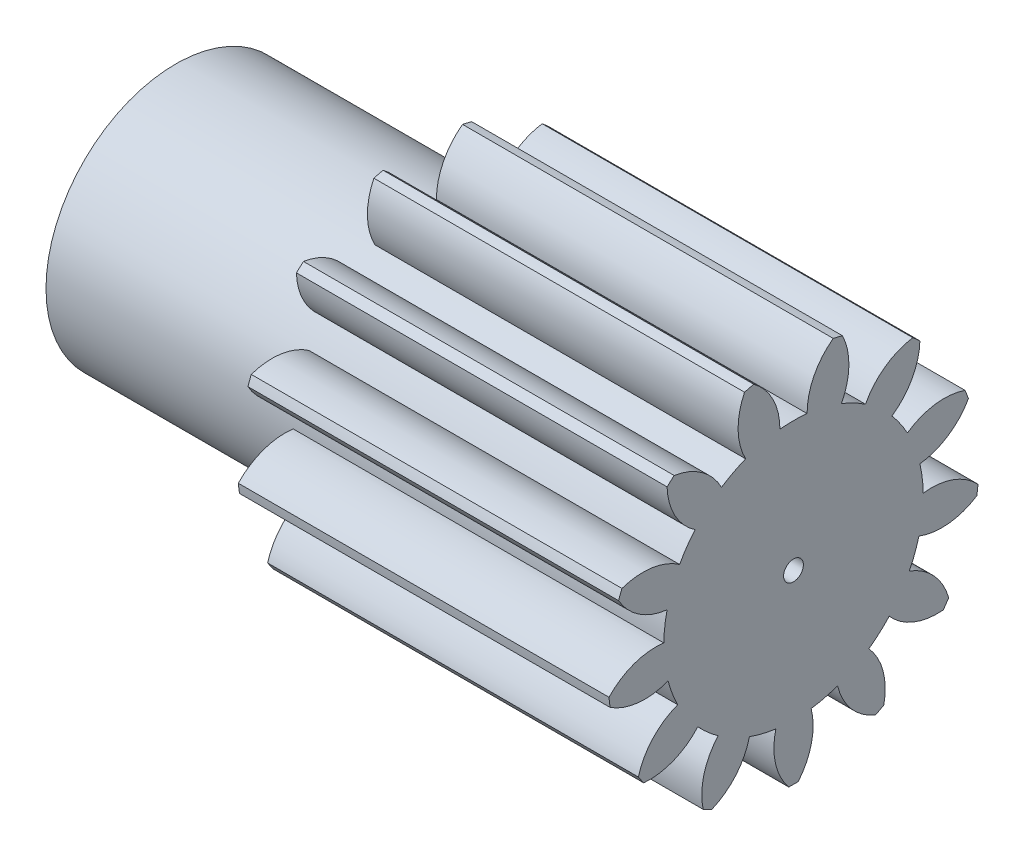
SolidWorks part; units mm, degrees
ref_plane "Plane1" through (0, 0, 0) normal (0, 0, 1) x (1, 0, 0)
ref_plane "Plane2" through (0, 0, 0) normal (0, 1, 0) x (1, 0, 0)
ref_plane "Plane3" through (0, 0, 0) normal (1, 0, 0) x (0, 0, -1)
sketch "HoldingSke" plane through (0, 0, 0) normal (0, 1, 0) x (1, 0, 0)
  line L0 (0, 0) -> (0.9744, -0.225)
  line L1 (-15, 0) -> (100, 0) construction
  line L2 (0, 0) -> (-2.1039, 2.3779)
  line L3 (0, 0) -> (-11.863, 4.5341)
  line L4 (0, 0) -> (8.4147, 1.9427)
  line L5 (0, 0) -> (-23.4238, -8.7364)
  line L6 (0, 0) -> (-12.4344, -8.3896)
  line L7 (-2.1039, 2.3779) -> (3.2774, 26.7919)
  line L8 (-76.2, 54.61) -> (-76.1, 54.61)
  line L9 (-71.009, 38.7566) -> (-53.1078, 45.2721)
  line L10 (-76.2, 71.12) -> (104.1128, 71.12)
  line L11 (0, 0) -> (-15, 0)
  line L12 (-76.2, 101.6) -> (-76.162, 101.6)
  line L13 (24.9733, 27.94) -> (52.9518, 28.4284)
  line L14 (24.9733, 27.94) -> (24.9743, 27.94)
  line L15 (24.9733, 27.94) -> (100.4006, 29.5858)
  line L16 (-63.627, -1) -> (-12.827, -1)
  circle A0 centre (0, 0) radius 0.4
  circle A1 centre (0, 0) radius 5.249
  circle A2 centre (0, 0) radius 37.5
  circle A3 centre (0, 0) radius 0.4
  dimension "MHD" = 10.498
  dimension "Hub_dia" = 75
  dimension "Bore" = 0.8
  dimension "MBD" = 0.8
  dimension "Num_teeth" = 13
  dimension "Pitch" = 1
  dimension "Overall_len" = 25
  dimension "Show_teeth" = 13
  dimension "Thickness" = 15
  dimension "OAL" = 25.0001
  dimension "T_dim" = 0.1
  dimension "Ap" = 20
  dimension "H" = 19.05
  dimension "Pitch_radius" = 180.3128
  dimension "Width" = 15
  dimension "Backlash" = 0.038
  dimension "Addendum_fac" = 1
  dimension "Dedendum_fac" = 1.25
  dimension "Clearance_fac" = 0.25
  dimension "Dedendum_add" = 0.001
  dimension "Module" = 1
sketch "BasProSke" plane through (0, 0, 0) normal (0, 1, 0) x (1, 0, 0)
  line L0 (-10, 0) -> (60, 0) construction
  line L1 (0, 0) -> (0, 7.5)
  line L2 (0, 0) -> (15, 0)
  line L3 (15, 0) -> (15, 7.5)
  line L4 (15, 7.5) -> (0, 7.5)
  dimension "Thickness" = 15
  dimension "Diameter" = 15
revolve "Base-Revolve" add sketch "BasProSke" angle 360 about L0
sketch "TooCutSke" plane through (0, 0, 0) normal (1, 0, 0) x (0, 0, -1)
  line L1 (0, 0) -> (0, 107) construction
  line L2 (0, 0) -> (-0.8499, 6.4442) construction
  line L3 (0, 0) -> (-3.0921, 12.5452) construction
  line L4 (-0.8499, 6.4442) -> (-1.5461, 6.2726) construction
  arc A0 (0.5505, 5.2201) -> (-0.5505, 5.2201) centre (0, 0) ccw
  arc A1 (1.6352, 7.3456) -> (-1.6352, 7.3456) centre (0, 0) ccw
  circle A2 centre (0, 0) radius 6.5 construction
  circle A3 centre (0, 0) radius 6.108 construction
  arc A4 (-0.5505, 5.2201) -> (-1.6352, 7.3456) centre (-3.1505, 5.2328) ccw
  arc A5 (1.6352, 7.3456) -> (0.5505, 5.2201) centre (3.1505, 5.2328) ccw
  dimension "Root_dia" = 10.498
  dimension "Overcut_dia" = 15.0508
  dimension "Pitch_dia" = 13
  dimension "Base_dia" = 12.216
  dimension "Flank_rad" = 2.6
  dimension "Half_ang" = 13.846
  dimension "Half_CT" = 0.717
extrude "ToothCut" cut sketch "TooCutSke" along normal through all
fillet "Breaks" [suppressed] radius 0.02
fillet "RootFillets" [suppressed] radius 0.251
pattern_circular "TeethCuts" count 13 every 27.692 about axis through (-10, 0, 0) along (1, 0, 0) of "ToothCut", "RootFillets", "Breaks"
sketch "HubNeaOneSke" plane through (0, 0, 0) normal (-1, 0, 0) x (0, 0, 1)
  circle A0 centre (0, 0) radius 5.249
  dimension "Diameter" = 10.498
extrude "HubNearOne" add sketch "HubNeaOneSke" along normal blind 10.0001
sketch "HubNeaBotSke" plane through (0, 0, 0) normal (-1, 0, 0) x (0, 0, 1)
  circle A0 centre (0, 0) radius 5.249
  dimension "Diameter" = 10.498
extrude "HubNearBoth" [suppressed] add sketch "HubNeaBotSke" along normal blind 5
ref_plane "FarPln" through (15, 0, 0) normal (1, 0, 0) x (0, 0, -1)
sketch "HubFarSke" plane through (15, 0, 0) normal (1, 0, 0) x (0, 0, -1)
  circle A0 centre (0, 0) radius 5.249
  dimension "Diameter" = 10.498
extrude "HubFar" [suppressed] add sketch "HubFarSke" along normal blind 5
sketch "BorSke" plane through (0, 0, 0) normal (1, 0, 0) x (0, 0, -1)
  circle A0 centre (0, 0) radius 0.4
  dimension "Diameter" = 0.8
extrude "Bore" cut sketch "BorSke" along normal mid plane 50.0001
sketch "KeySke" plane through (0, 0, 0) normal (1, 0, 0) x (0, 0, -1)
  line L0 (-0.05, 0) -> (-0.05, 0.5)
  line L1 (-0.05, 0.5) -> (0.05, 0.5)
  line L2 (0.05, 0.5) -> (0.05, 0)
  line L3 (0, 0) -> (0, 34) construction
  line L4 (-0.05, 0) -> (0.05, 0)
  dimension "Offset" = 0.5
  dimension "Width" = 0.1
extrude "Keyway" [suppressed] cut sketch "KeySke" along normal mid plane 50.0001
pattern_circular "Keyway2" [suppressed] count 2 every 90 about axis through (-10, 0, 0) along (1, 0, 0)
equation "' \"Module@HoldingSke\" = 6.35"
equation "' \"Num_teeth@HoldingSke\" = 12"
equation "' \"Ap@HoldingSke\" =  20"
equation "' \"Ap@HoldingSke\" = 20"
equation "' \"Width@HoldingSke\" = 0.5 * 25.4"
equation "' \"Hub_dia@HoldingSke\"= 1 * 25.4"
equation "' \"Hub_dia@HoldingSke\" = 1 * 25.4"
equation "' \"Overall_len@HoldingSke\" = 1.0 * 25.4"
equation "' \"Bore@HoldingSke\" = 0.75 * 25.4"
equation "' \"T_dim@HoldingSke\" = 0.1 * 25.4"
equation "' \"Width@KeySke\" = 0.25 * 25.4"
equation "' \"Show_teeth@HoldingSke\" = 13"
equation "' \"Backlash@HoldingSke\" = 0.009 * 25.4"
equation "' \"Addendum_fac@HoldingSke\" = 1.0"
equation "' \"Dedendum_fac@HoldingSke\" = 1.25"
equation "' \"Dedendum_add@HoldingSke\" = 0.00005 * 25.4"
equation "' \"Clearance_fac@HoldingSke\" = 0.25"
equation "\"Pitch@HoldingSke\" = 1 / \"Module@HoldingSke\""
equation "\"Overcut_dia@TooCutSke\" = (\"Num_teeth@HoldingSke\" + 2 * \"Addendum_fac@HoldingSke\") / \"Pitch@HoldingSke\" + 0.002 * 25.4"
equation "\"Pitch_dia@TooCutSke\" = \"Num_teeth@HoldingSke\" / \"Pitch@HoldingSke\""
equation "\"Base_dia@TooCutSke\" = \"Num_teeth@HoldingSke\" / \"Pitch@HoldingSke\" * cos((\"Ap@HoldingSke\"  * 3.14159265 / 180))"
equation "\"Root_dia@TooCutSke\" = (\"Num_teeth@HoldingSke\" + 2) / \"Pitch@HoldingSke\" - 2 * (\"Addendum_fac@HoldingSke\" + \"Dedendum_fac@HoldingSke\") / \"Pitch@HoldingSke\" - \"Dedendum_add@HoldingSke\" * 2"
equation "\"Half_ang@TooCutSke\" = 180 / \"Num_teeth@HoldingSke\""
equation "\"Half_CT@TooCutSke\" = \"Num_teeth@HoldingSke\" / \"Pitch@HoldingSke\" * sin((3.14159265 / 2 / \"Num_teeth@HoldingSke\")) / 2 - 7 * \"Backlash@HoldingSke\" / 4"
equation "\"Flank_rad@TooCutSke\" = \"Num_teeth@HoldingSke\" / \"Pitch@HoldingSke\" / 5"
equation "\"Radius@RootFillets\" = \"Clearance_fac@HoldingSke\" / \"Pitch@HoldingSke\" + \"Dedendum_add@HoldingSke\""
equation "\"Break_rad@Breaks\" = 0.02 / \"Pitch@HoldingSke\""
equation "\"Thickness@HoldingSke\" = \"Width@HoldingSke\""
equation "\"OAL@HoldingSke\" = \"Thickness@HoldingSke\""
equation "\"MHD@HoldingSke\" = (\"Num_teeth@HoldingSke\" + 2) / \"Pitch@HoldingSke\" - 2 * (\"Addendum_fac@HoldingSke\" + \"Dedendum_fac@HoldingSke\")  / \"Pitch@HoldingSke\" - \"Dedendum_add@HoldingSke\" * 2"
equation "\"MBD@HoldingSke\" = (\"Num_teeth@HoldingSke\" + 2) / \"Pitch@HoldingSke\" - 2 * (\"Addendum_fac@HoldingSke\" + \"Dedendum_fac@HoldingSke\")  / \"Pitch@HoldingSke\" - \"Dedendum_add@HoldingSke\" * 2 - 0.002 * 25.4"
equation "\"MHD@HoldingSke\" = ((sgn( \"MHD@HoldingSke\" - \"Hub_dia@HoldingSke\" )-1)*( \"MHD@HoldingSke\" - \"Hub_dia@HoldingSke\" ))/-2+ \"Hub_dia@HoldingSke\""
equation "\"MBD@HoldingSke\" = ((sgn( \"MBD@HoldingSke\" - \"Bore@HoldingSke\" )-1)*( \"MBD@HoldingSke\" - \"Bore@HoldingSke\" ))/-2+ \"Bore@HoldingSke\""
equation "\"OAL@HoldingSke\" = ((sgn( \"OAL@HoldingSke\" - \"Overall_len@HoldingSke\" )+1)*( \"OAL@HoldingSke\" - \"Overall_len@HoldingSke\" ))/2 + \"Overall_len@HoldingSke\" + 0.000002 * 25.4"
equation "\"Num_teeth@TeethCuts\" = int( \"Show_teeth@HoldingSke\" ) + 1"
equation "\"Num_teeth@TeethCuts\" = ((sgn( \"Num_teeth@TeethCuts\" - \"Num_teeth@HoldingSke\" )-1)*( \"Num_teeth@TeethCuts\" - \"Num_teeth@HoldingSke\" ))/-2+ \"Num_teeth@HoldingSke\""
equation "\"Num_teeth@TeethCuts\" = ((sgn( \"Num_teeth@TeethCuts\" - 2.0)+1)*( \"Num_teeth@TeethCuts\" - 2.0))/2 +2.0"
equation "\"Angle@TeethCuts\" = 360.0 / \"Num_teeth@HoldingSke\""
equation "\"Diameter@BasProSke\" = (\"Num_teeth@HoldingSke\" + 2 * \"Addendum_fac@HoldingSke\") / \"Pitch@HoldingSke\""
equation "\"Thickness@BasProSke\"  = \"Thickness@HoldingSke\""
equation "' \"Fillet_rad@BasProSke\" =  \"Thickness@HoldingSke\" * 0.05"
equation "' \"Fillet_rad@BasProSke\" = \"Thickness@HoldingSke\" * 0.05"
equation "\"MHD@HoldingSke\" = ((sgn( \"MHD@HoldingSke\" - \"Root_dia@TooCutSke\" )-1)*( \"MHD@HoldingSke\" - \"Root_dia@TooCutSke\" ))/-2+ \"Root_dia@TooCutSke\""
equation "\"Diameter@HubNeaOneSke\" = \"MHD@HoldingSke\""
equation "\"Length@HubNearOne\" = \"OAL@HoldingSke\" - \"Thickness@BasProSke\""
equation "\"Diameter@HubNeaBotSke\" = \"MHD@HoldingSke\""
equation "\"Length@HubNearBoth\" = ( \"OAL@HoldingSke\" - \"Thickness@BasProSke\" ) / 2.0"
equation "\"Thickness@FarPln\" = \"Thickness@BasProSke\""
equation "\"Diameter@HubFarSke\" = \"MHD@HoldingSke\""
equation "\"Length@HubFar\" = ( \"OAL@HoldingSke\" - \"Thickness@BasProSke\" ) / 2.0"
equation "\"Diameter@BorSke\" = \"MBD@HoldingSke\""
equation "\"D1@Bore\" = \"OAL@HoldingSke\" * 2.0"
equation "\"D1@Keyway\" = \"OAL@HoldingSke\" * 2.0"
equation "\"Offset@KeySke\" = \"T_dim@HoldingSke\" + \"MBD@HoldingSke\" / 2.0"
